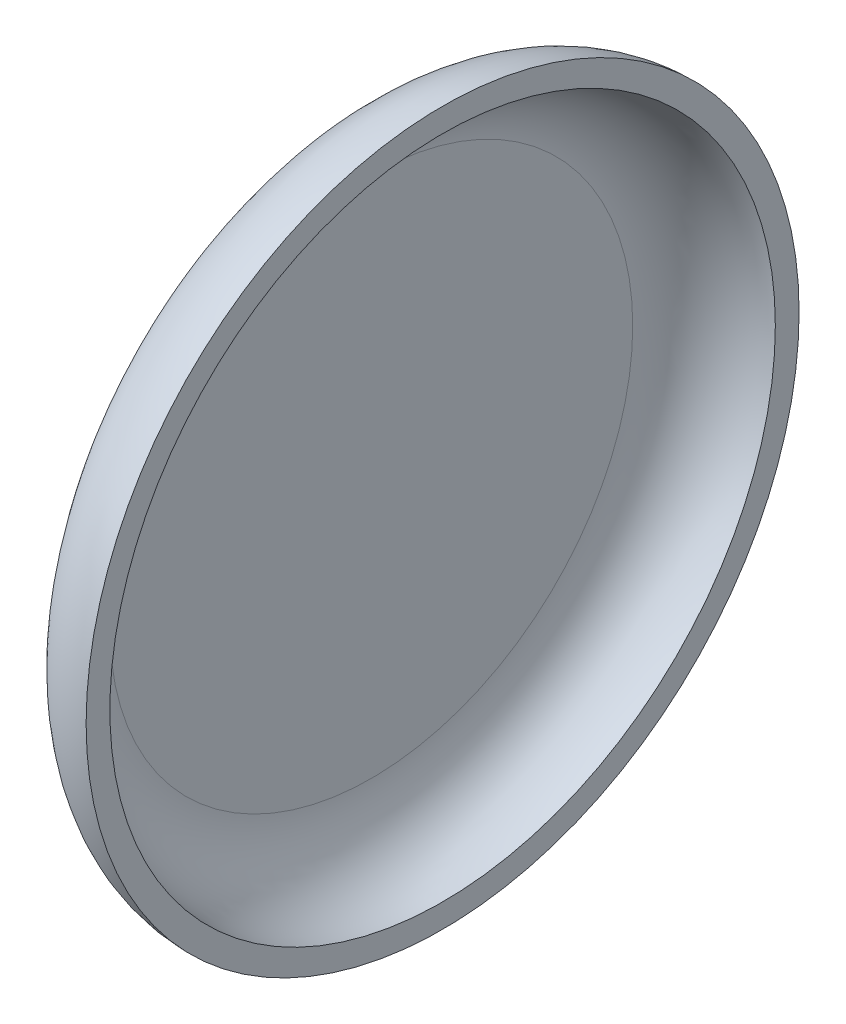
SolidWorks part; units mm, degrees
ref_plane "Front Plane" through (0, 0, 0) normal (0, 0, 1) x (1, 0, 0)
ref_plane "Top Plane" through (0, 0, 0) normal (0, 1, 0) x (1, 0, 0)
ref_plane "Right Plane" through (0, 0, 0) normal (1, 0, 0) x (0, 0, -1)
sketch "Sketch1" plane through (0, 0, 0) normal (0, 0, 1) x (1, 0, 0)
  line L0 (0, 12.7584) -> (0, 0) construction
  line L1 (0, 0) -> (-15.5791, 0) construction
  line L2 (-4, 11) -> (-4, 0)
  line L3 (-4, 0) -> (-4, 11)
  line L4 (0, 15) -> (0, 12.7584) construction
  line L5 (-3, 11) -> (-3, 0)
  line L6 (0, 15) -> (0, 14)
  line L7 (-4, 0) -> (-3, 0)
  line L8 (-3, 0) -> (-4, 0)
  line L9 (-3, 0) -> (-4, 0)
  arc A0 (-4, 11) -> (0, 15) centre (0, 11) cw
  arc A1 (-3, 11) -> (0, 14) centre (0, 11) cw
  dimension "D1" = 15
  dimension "D2" = 4
  dimension "D3" = 1
  dimension "D4" = 1
revolve "Revolve1" add sketch "Sketch1" angle 360 about L1
